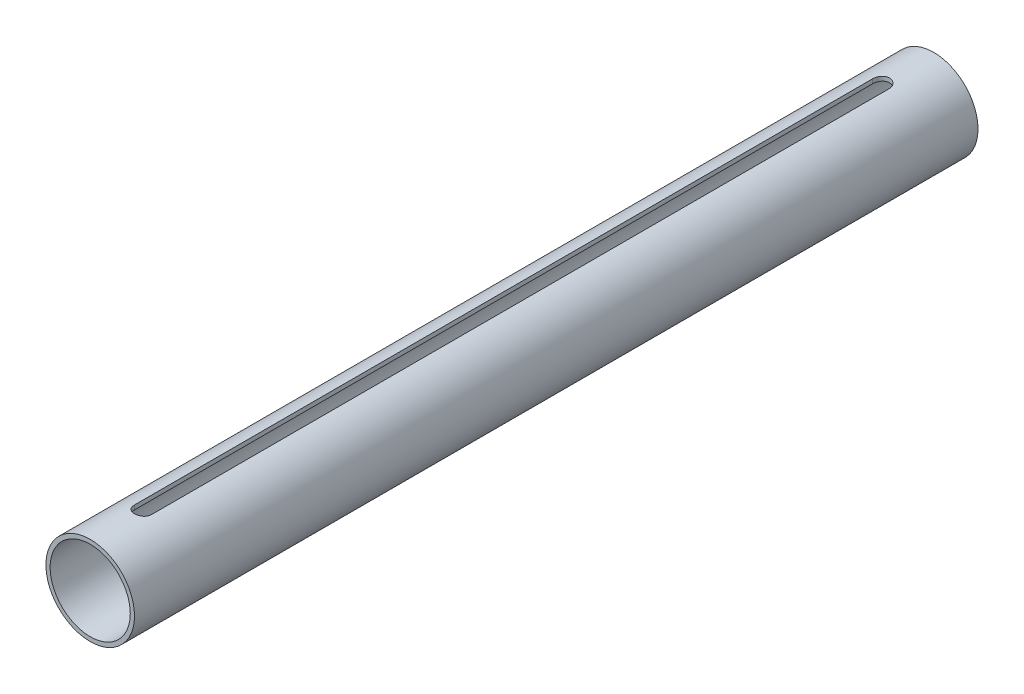
SolidWorks part; units mm, degrees
ref_plane "Front Plane" through (0, 0, 0) normal (0, 0, 1) x (1, 0, 0)
ref_plane "Top Plane" through (0, 0, 0) normal (0, 1, 0) x (1, 0, 0)
ref_plane "Right Plane" through (0, 0, 0) normal (1, 0, 0) x (0, 0, -1)
sketch "Sketch1" plane through (0, 0, 0) normal (0, 0, 1) x (1, 0, 0)
  line L0 (0, 22.3652) -> (0, -23.5462) construction
  circle A0 centre (0, 0) radius 19
  circle A1 centre (0, 0) radius 21
  dimension "D1" = 38
  dimension "D2" = 2
extrude "Boss-Extrude1" add sketch "Sketch1" along normal mid plane 400
ref_plane "Plane1" through (0, 22, 0) normal (0, 1, 0) x (1, 0, 0)
sketch "Sketch2" plane through (0, 22, 0) normal (0, 1, 0) x (1, 0, 0)
  line L0 (0, 0) -> (0, -608.2141) construction
  line L1 (0, -175) -> (0, 175) construction
  line L2 (-4, -175) -> (-4, 175)
  line L3 (4, -175) -> (4, 175)
  arc A0 (-4, -175) -> (4, -175) centre (0, -175) ccw
  arc A1 (4, 175) -> (-4, 175) centre (0, 175) ccw
  point P5 (0, 0)
  dimension "D1" = 350
  dimension "D2" = 8
extrude "Cut-Extrude1" cut sketch "Sketch2" against normal up to next
